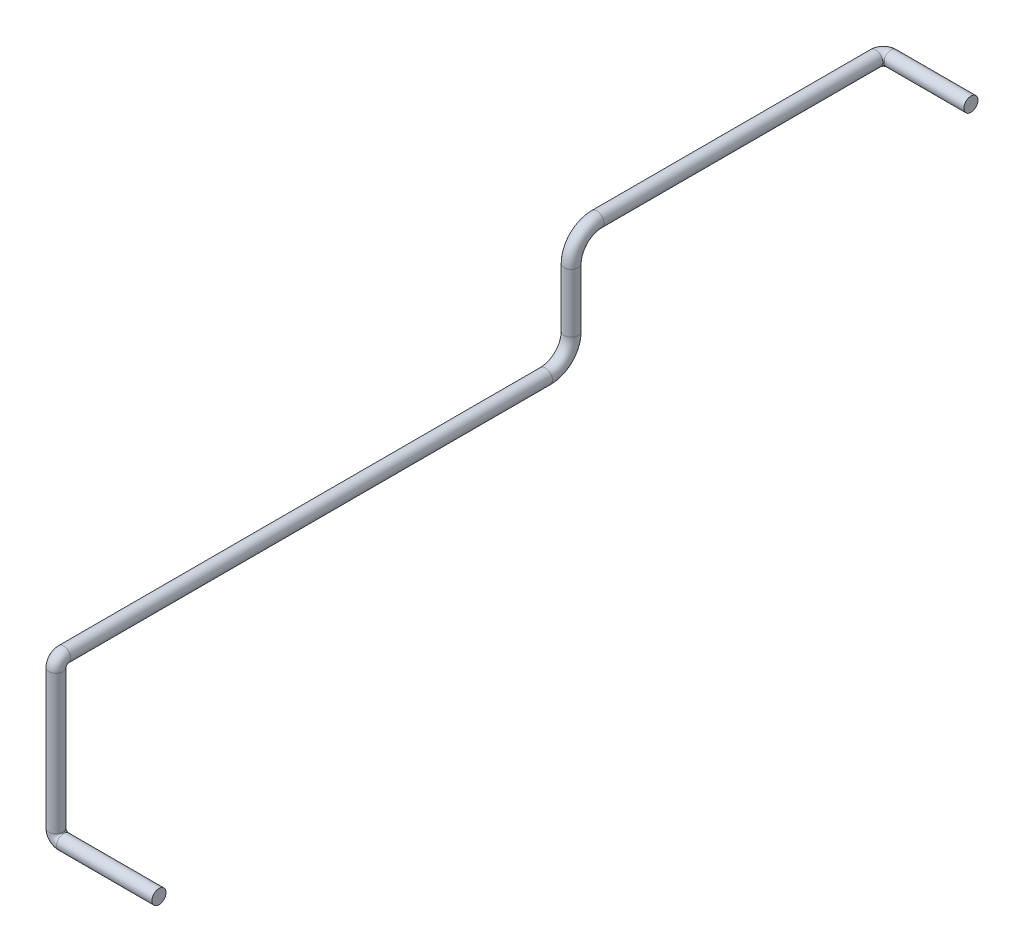
SolidWorks part; units mm, degrees
ref_plane "Alzado" through (0, 0, 0) normal (0, 0, 1) x (1, 0, 0)
ref_plane "Planta" through (0, 0, 0) normal (0, 1, 0) x (1, 0, 0)
ref_plane "Vista lateral" through (0, 0, 0) normal (1, 0, 0) x (0, 0, -1)
sketch3d "Croquis3D1"
  line L0 (0, 0, 0) -> (-185, 0, 0)
  line L1 (-200, 15, 0) -> (-200, 285, 0)
  line L2 (-200, 514, -1050) -> (-200, 514, -1591)
  line L3 (-185, 514, -1606) -> (-30, 514, -1606)
  line L4 (-200, 300, -15) -> (-200, 300, -950)
  line L5 (-200, 464, -1000) -> (-200, 350, -1000)
  arc A0 (-200, 300, -15) -> (-200, 285, 0) centre (-200, 285, -15) ccw
  arc A1 (-185, 0, 0) -> (-200, 15, 0) centre (-185, 15, 0) ccw
  arc A2 (-200, 464, -1000) -> (-200, 514, -1050) centre (-200, 464, -1050) ccw
  arc A3 (-200, 350, -1000) -> (-200, 300, -950) centre (-200, 350, -950) ccw
  arc A4 (-200, 514, -1591) -> (-185, 514, -1606) centre (-185, 514, -1591) ccw
  point P10 (-200, 300, 0)
  point P11 (-185, 285, -15)
  point P14 (-200, 0, 0)
  point P15 (-185, 15, -15)
  point P18 (-200, 514, -1000)
  point P19 (-250, 464, -1050)
  point P22 (-200, 300, -1000)
  point P23 (-250, 350, -950)
  point P26 (-200, 514, -1606)
  point P27 (-185, 499, -1591)
  dimension "D6" = 15
  dimension "D7" = 50
  dimension "D8" = 15
  dimension "D1" = 200
  dimension "D2" = 300
  dimension "D5" = 606
  dimension "D3" = 1000
  dimension "D4" = 170
  dimension "D9" = 214
sketch "Croquis1" plane through (0, 0, 0) normal (1, 0, 0) x (0, 0, -1)
  circle A0 centre (0, 0) radius 13.7
  dimension "D1" = 27.4
sweep "Barrer1" add profiles "Croquis1" path "Croquis3D1"
